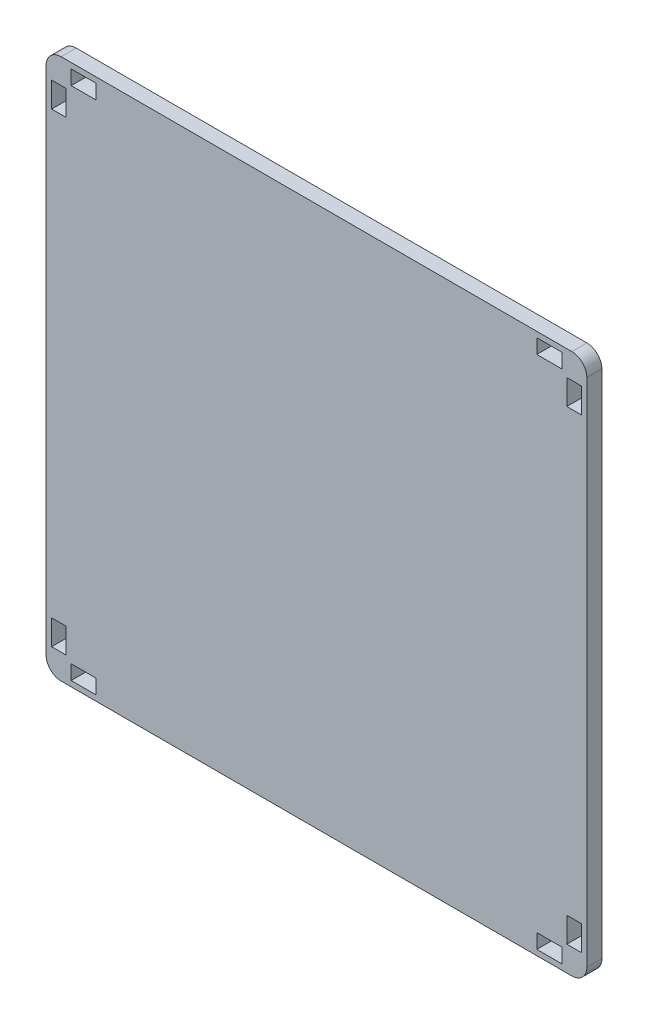
SolidWorks part; units mm, degrees
ref_plane "前视基准面" through (0, 0, 0) normal (0, 0, 1) x (1, 0, 0)
ref_plane "上视基准面" through (0, 0, 0) normal (0, 1, 0) x (1, 0, 0)
ref_plane "右视基准面" through (0, 0, 0) normal (1, 0, 0) x (0, 0, -1)
sketch "草图2" plane through (0, 0, 0) normal (0, 0, 1) x (1, 0, 0)
  line L13 (1, 0) -> (6, 0)
  line L14 (0, 1) -> (0, 6)
  line L15 (1, 100) -> (6, 100)
  line L16 (100, 1) -> (100, 6)
  line L17 (99, 0) -> (94, 0)
  line L19 (99, -2.9) -> (94, -2.9)
  line L20 (94, 0) -> (94, -2.9)
  line L21 (99, 0) -> (99, -2.9)
  line L23 (94, 0) -> (99, 0)
  line L24 (100, 1) -> (102.9, 1)
  line L25 (100, 1) -> (100, 6)
  line L26 (100, 6) -> (102.9, 6)
  line L27 (102.9, 1) -> (102.9, 6)
  line L29 (100, 99) -> (102.9, 99)
  line L30 (100, 99) -> (100, 94)
  line L31 (100, 94) -> (102.9, 94)
  line L32 (102.9, 99) -> (102.9, 94)
  line L34 (99, 100) -> (94, 100)
  line L35 (99, 100) -> (99, 102.9)
  line L36 (99, 102.9) -> (94, 102.9)
  line L37 (94, 100) -> (94, 102.9)
  line L39 (1, 0) -> (6, 0)
  line L40 (1, 0) -> (1, -2.9)
  line L41 (1, -2.9) -> (6, -2.9)
  line L42 (6, 0) -> (6, -2.9)
  line L44 (0, 1) -> (-2.9, 1)
  line L45 (0, 1) -> (0, 6)
  line L46 (0, 6) -> (-2.9, 6)
  line L47 (-2.9, 1) -> (-2.9, 6)
  line L49 (1, 100) -> (6, 100)
  line L50 (1, 100) -> (1, 102.9)
  line L51 (1, 102.9) -> (6, 102.9)
  line L52 (6, 100) -> (6, 102.9)
  line L53 (100, 94) -> (100, 99)
  line L54 (0, 99) -> (-2.9, 99)
  line L55 (0, 99) -> (0, 94)
  line L56 (0, 94) -> (-2.9, 94)
  line L57 (-2.9, 99) -> (-2.9, 94)
  line L58 (94, 100) -> (99, 100)
  line L59 (0, 94) -> (0, 99)
  line L64 (101, 104) -> (-1, 104)
  line L65 (104, 101) -> (104, -1)
  line L66 (101, -4) -> (-1, -4)
  line L67 (-4, 101) -> (-4, -1)
  arc A0 (-4, -1) -> (-1, -4) centre (-1, -1) ccw
  arc A1 (101, -4) -> (104, -1) centre (101, -1) ccw
  arc A2 (104, 101) -> (101, 104) centre (101, 101) ccw
  arc A3 (-4, 101) -> (-1, 104) centre (-1, 101) cw
extrude "凸台-拉伸4" add sketch "草图2" along normal blind 3 contours L64 L67 L66 L65 L44 L47 L46 L14 L13 L42 L41 L40 L34 L37 L36 L35 L29 L32 L31 L30 L17 L21 L19 L20 L27 L24 L16 L26 L52 L15 L50 L51 L57 L54 L55 L56
